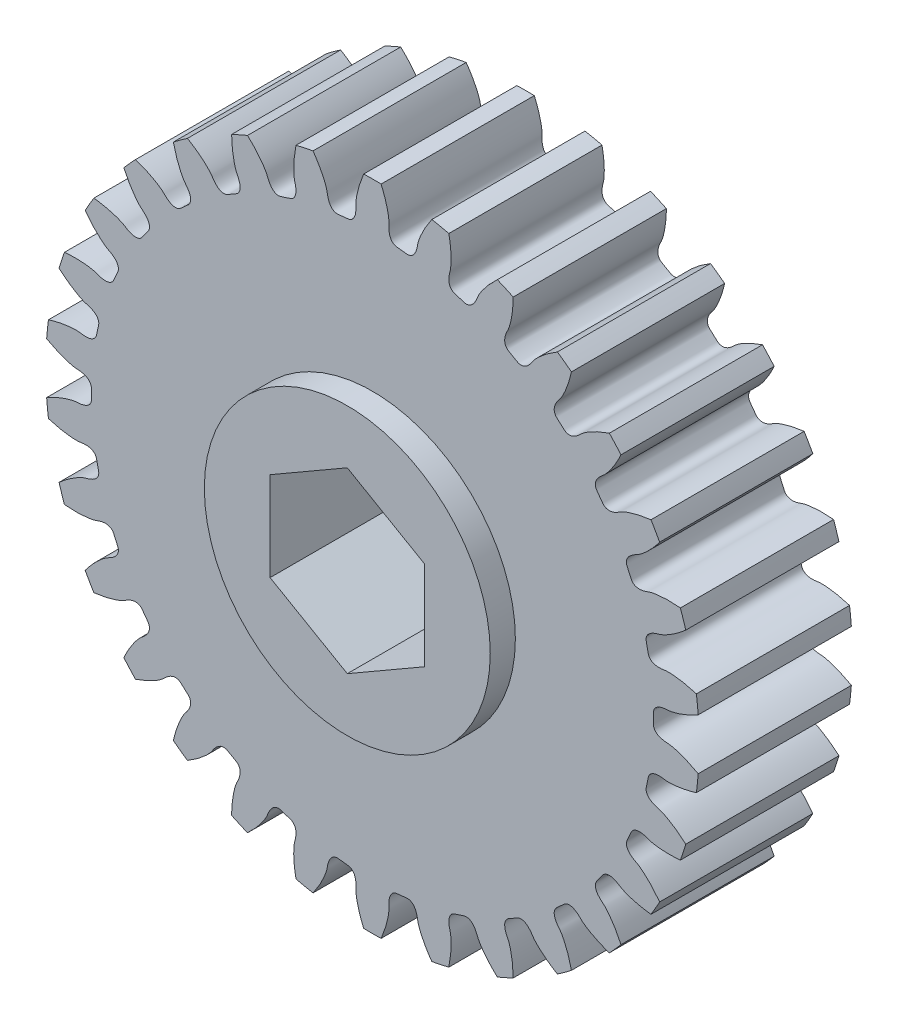
SolidWorks part; units mm, degrees
material "7075-T6 (SN)"
ref_plane "Front Plane" through (0, 0, 0) normal (0, 0, 1) x (1, 0, 0)
ref_plane "Top Plane" through (0, 0, 0) normal (0, 1, 0) x (1, 0, 0)
ref_plane "Right Plane" through (0, 0, 0) normal (1, 0, 0) x (0, 0, -1)
ref_plane "Plane1" through (0, 0, 4.7625) normal (0, 0, 1) x (1, 0, 0)
sketch "Sketch1" plane through (0, 0, 4.7625) normal (0, 0, 1) x (1, 0, 0)
  arc A0 (20.258, 1.5856) -> (20.145, 2.661) centre (0, 0) ccw
  arc A1 (19.4857, 5.7628) -> (19.1516, 6.7912) centre (0, 0) ccw
  arc A2 (17.8617, 9.6882) -> (17.3211, 10.6246) centre (0, 0) ccw
  arc A3 (15.4571, 13.1901) -> (14.7336, 13.9937) centre (0, 0) ccw
  arc A4 (12.377, 16.1156) -> (11.5022, 16.7512) centre (0, 0) ccw
  arc A5 (8.7559, 18.3368) -> (7.768, 18.7766) centre (0, 0) ccw
  arc A6 (4.7521, 19.7565) -> (3.6944, 19.9813) centre (0, 0) ccw
  arc A7 (0.5407, 20.3128) -> (-0.5407, 20.3128) centre (0, 0) ccw
  arc A8 (-3.6944, 19.9813) -> (-4.7521, 19.7565) centre (0, 0) ccw
  arc A9 (-7.768, 18.7766) -> (-8.7559, 18.3368) centre (0, 0) ccw
  arc A10 (-11.5022, 16.7512) -> (-12.377, 16.1156) centre (0, 0) ccw
  arc A11 (-14.7336, 13.9937) -> (-15.4571, 13.1901) centre (0, 0) ccw
  arc A12 (-17.3211, 10.6246) -> (-17.8617, 9.6882) centre (0, 0) ccw
  arc A13 (-19.1516, 6.7912) -> (-19.4857, 5.7628) centre (0, 0) ccw
  arc A14 (-20.145, 2.661) -> (-20.258, 1.5856) centre (0, 0) ccw
  arc A15 (-20.258, -1.5856) -> (-20.145, -2.661) centre (0, 0) ccw
  arc A16 (-19.4857, -5.7628) -> (-19.1516, -6.7912) centre (0, 0) ccw
  arc A17 (-17.8617, -9.6882) -> (-17.3211, -10.6246) centre (0, 0) ccw
  arc A18 (-15.4571, -13.1901) -> (-14.7336, -13.9937) centre (0, 0) ccw
  arc A19 (-12.377, -16.1156) -> (-11.5022, -16.7512) centre (0, 0) ccw
  arc A20 (-8.7559, -18.3368) -> (-7.768, -18.7766) centre (0, 0) ccw
  arc A21 (-4.7521, -19.7565) -> (-3.6944, -19.9813) centre (0, 0) ccw
  arc A22 (-0.5407, -20.3128) -> (0.5407, -20.3128) centre (0, 0) ccw
  arc A23 (3.6944, -19.9813) -> (4.7521, -19.7565) centre (0, 0) ccw
  arc A24 (7.768, -18.7766) -> (8.7559, -18.3368) centre (0, 0) ccw
  arc A25 (11.5022, -16.7512) -> (12.377, -16.1156) centre (0, 0) ccw
  arc A26 (14.7336, -13.9937) -> (15.4571, -13.1901) centre (0, 0) ccw
  arc A27 (17.3211, -10.6246) -> (17.8617, -9.6882) centre (0, 0) ccw
  arc A28 (19.1516, -6.7912) -> (19.4857, -5.7628) centre (0, 0) ccw
  arc A29 (20.145, -2.661) -> (20.258, -1.5856) centre (0, 0) ccw
  spline S0 degree 3 number of poles 93 (20.258, 1.5856) -> (20.258, -1.5856)
  spline S1 degree 3 number of poles 93 (19.4857, 5.7628) -> (20.145, 2.661)
  spline S2 degree 3 number of poles 93 (17.8617, 9.6882) -> (19.1516, 6.7912)
  spline S3 degree 3 number of poles 93 (15.4571, 13.1901) -> (17.3211, 10.6246)
  spline S4 degree 3 number of poles 93 (12.377, 16.1156) -> (14.7336, 13.9937)
  spline S5 degree 3 number of poles 93 (8.7559, 18.3368) -> (11.5022, 16.7512)
  spline S6 degree 3 number of poles 93 (4.7521, 19.7565) -> (7.768, 18.7766)
  spline S7 degree 3 number of poles 93 (0.5407, 20.3128) -> (3.6944, 19.9813)
  spline S8 degree 3 number of poles 93 (-3.6944, 19.9813) -> (-0.5407, 20.3128)
  spline S9 degree 3 number of poles 93 (-7.768, 18.7766) -> (-4.7521, 19.7565)
  spline S10 degree 3 number of poles 93 (-11.5022, 16.7512) -> (-8.7559, 18.3368)
  spline S11 degree 3 number of poles 93 (-14.7336, 13.9937) -> (-12.377, 16.1156)
  spline S12 degree 3 number of poles 93 (-17.3211, 10.6246) -> (-15.4571, 13.1901)
  spline S13 degree 3 number of poles 93 (-19.1516, 6.7912) -> (-17.8617, 9.6882)
  spline S14 degree 3 number of poles 93 (-20.145, 2.661) -> (-19.4857, 5.7628)
  spline S15 degree 3 number of poles 93 (-20.258, -1.5856) -> (-20.258, 1.5856)
  spline S16 degree 3 number of poles 93 (-19.4857, -5.7628) -> (-20.145, -2.661)
  spline S17 degree 3 number of poles 93 (-17.8617, -9.6882) -> (-19.1516, -6.7912)
  spline S18 degree 3 number of poles 93 (-15.4571, -13.1901) -> (-17.3211, -10.6246)
  spline S19 degree 3 number of poles 93 (-12.377, -16.1156) -> (-14.7336, -13.9937)
  spline S20 degree 3 number of poles 93 (-8.7559, -18.3368) -> (-11.5022, -16.7512)
  spline S21 degree 3 number of poles 93 (-4.7521, -19.7565) -> (-7.768, -18.7766)
  spline S22 degree 3 number of poles 93 (-0.5407, -20.3128) -> (-3.6944, -19.9813)
  spline S23 degree 3 number of poles 93 (3.6944, -19.9813) -> (0.5407, -20.3128)
  spline S24 degree 3 number of poles 93 (7.768, -18.7766) -> (4.7521, -19.7565)
  spline S25 degree 3 number of poles 93 (11.5022, -16.7512) -> (8.7559, -18.3368)
  spline S26 degree 3 number of poles 93 (14.7336, -13.9937) -> (12.377, -16.1156)
  spline S27 degree 3 number of poles 93 (17.3211, -10.6246) -> (15.4571, -13.1901)
  spline S28 degree 3 number of poles 93 (19.1516, -6.7912) -> (17.8617, -9.6882)
  spline S29 degree 3 number of poles 93 (20.145, -2.661) -> (19.4857, -5.7628)
extrude "Boss-Extrude1" add sketch "Sketch1" against normal blind 9.525
sketch "Sketch2" plane through (0, 0, 4.7625) normal (0, 0, 1) x (1, 0, 0)
  circle A0 centre (0, 0) radius 8.89
extrude "Boss-Extrude2" add sketch "Sketch2" along normal blind 1.5621
sketch "Sketch3" plane through (0, 0, -4.7625) normal (0, 0, -1) x (-1, 0, 0)
  circle A0 centre (0, 0) radius 8.89
extrude "Boss-Extrude3" add sketch "Sketch3" along normal blind 1.5621
sketch "Sketch4" plane through (0, 0, -6.3246) normal (0, 0, -1) x (-1, 0, 0)
  line L0 (4.8006, 2.7716) -> (0, 5.5433)
  line L1 (0, 5.5433) -> (-4.8006, 2.7716)
  line L2 (-4.8006, 2.7716) -> (-4.8006, -2.7716)
  line L3 (-4.8006, -2.7716) -> (0, -5.5433)
  line L4 (0, -5.5433) -> (4.8006, -2.7716)
  line L5 (4.8006, -2.7716) -> (4.8006, 2.7716)
extrude "Cut-Extrude1" cut sketch "Sketch4" against normal through all
